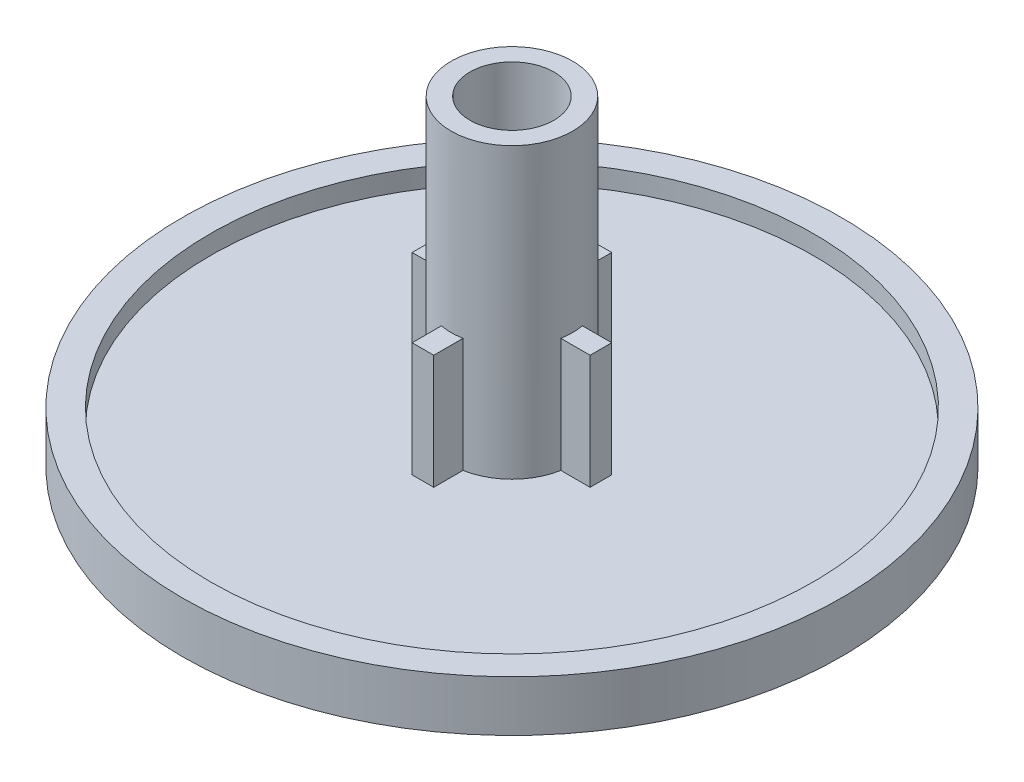
SolidWorks part; units mm, degrees
material "ABS"
ref_plane "Front Plane" through (0, 0, 0) normal (0, 0, 1) x (1, 0, 0)
ref_plane "Top Plane" through (0, 0, 0) normal (0, 1, 0) x (1, 0, 0)
ref_plane "Right Plane" through (0, 0, 0) normal (1, 0, 0) x (0, 0, -1)
sketch "Sketch1" plane through (0, 0, 0) normal (0, 1, 0) x (1, 0, 0)
  circle A0 centre (0, 0) radius 13.1699
  dimension "D1" = 26.3398
extrude "Boss-Extrude1" add sketch "Sketch1" along normal blind 1.27
sketch "Sketch2" plane through (0, 1.27, 0) normal (0, 1, 0) x (1, 0, 0)
  circle A0 centre (0, 0) radius 12.0523
  circle A1 centre (0, 0) radius 13.1699 construction
  circle A3 centre (0, 0) radius 13.1699
  circle A4 centre (0, 0) radius 13.1699
  dimension "D1" = 1.1176
  dimension "D2" = 0
extrude "Boss-Extrude2" add sketch "Sketch2" along normal blind 0.762
sketch "Sketch3" plane through (0, 1.27, 0) normal (0, 1, 0) x (1, 0, 0)
  circle A0 centre (0, 0) radius 2.4257
  dimension "D1" = 4.8514
extrude "Boss-Extrude3" add sketch "Sketch3" along normal blind 11.5443
sketch "Sketch6" plane through (0, 0, 0) normal (0, 0, 1) x (1, 0, 0)
  line L0 (13.1699, 2.032) -> (-13.1699, 2.032) construction
  line L1 (-3.556, 0) -> (3.556, 0)
  line L2 (-3.556, 0) -> (-3.556, 5.842)
  line L3 (-3.556, 5.842) -> (3.556, 5.842)
  line L4 (3.556, 0) -> (3.556, 5.842)
  line L5 (-3.556, 0) -> (3.556, 5.842) construction
  line L6 (-3.556, 5.842) -> (3.556, 0) construction
  line L7 (-13.1699, 0) -> (13.1699, 0) construction
  point P4 (0, 2.921)
  dimension "D1" = 7.112
  dimension "D2" = 3.81
extrude "Boss-Extrude4" add sketch "Sketch6" along normal mid plane 0.8636
sketch "Sketch7" plane through (0, 0, 0) normal (1, 0, 0) x (0, 0, -1)
  line L0 (-13.1699, 0) -> (13.1699, 0) construction
  line L1 (-3.556, 0) -> (3.556, 0)
  line L2 (-3.556, 0) -> (-3.556, 5.842)
  line L3 (-3.556, 5.842) -> (3.556, 5.842)
  line L4 (3.556, 0) -> (3.556, 5.842)
  line L5 (-3.556, 0) -> (3.556, 5.842) construction
  line L6 (-3.556, 5.842) -> (3.556, 0) construction
  line L7 (-0.4318, 5.842) -> (0.4318, 5.842) construction
  point P4 (0, 2.921)
  dimension "D1" = 7.112
extrude "Boss-Extrude5" add sketch "Sketch7" along normal mid plane 0.8636
sketch "Sketch4" plane through (0, 12.8143, 0) normal (0, 1, 0) x (1, 0, 0)
  circle A0 centre (0, 0) radius 1.6764
  dimension "D1" = 3.3528
extrude "Cut-Extrude1" cut sketch "Sketch4" against normal up to surface (11.5443 mm away) up to face at (0, 1.27, 12.0523)
